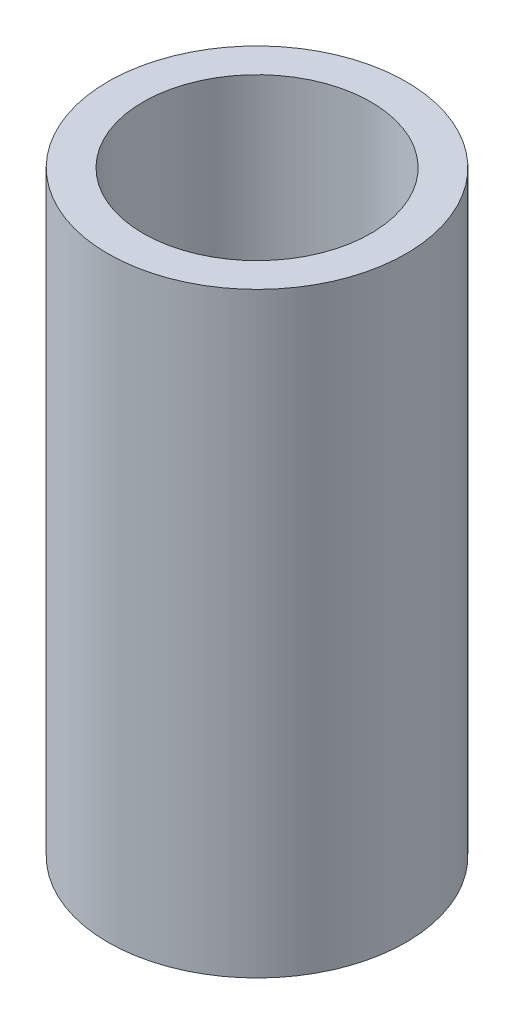
SolidWorks part; units mm, degrees
ref_plane "Front Plane" through (0, 0, 0) normal (0, 0, 1) x (1, 0, 0)
ref_plane "Top Plane" through (0, 0, 0) normal (0, 1, 0) x (1, 0, 0)
ref_plane "Right Plane" through (0, 0, 0) normal (1, 0, 0) x (0, 0, -1)
sketch "Sketch1" plane through (0, 0, 0) normal (0, 1, 0) x (1, 0, 0)
  circle A0 centre (0, 0) radius 43.6626
  circle A1 centre (0, 0) radius 57.15
  dimension "D1" = 87.3252
  dimension "D2" = 114.3
extrude "Extrude1" add sketch "Sketch1" along normal mid plane 228.6
equation "\"D1@Sketch1\" = \"D2@Sketch1\" - .531*2"
